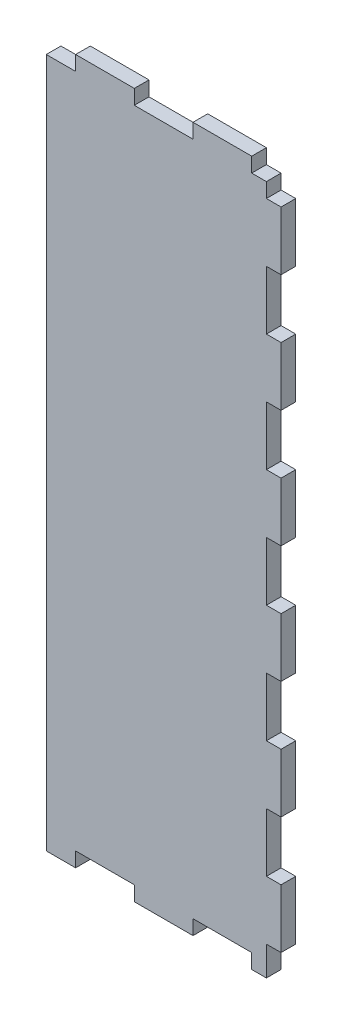
SolidWorks part; units mm, degrees
ref_plane "Front Plane" through (0, 0, 0) normal (0, 0, 1) x (1, 0, 0)
ref_plane "Top Plane" through (0, 0, 0) normal (0, 1, 0) x (1, 0, 0)
ref_plane "Right Plane" through (0, 0, 0) normal (1, 0, 0) x (0, 0, -1)
sketch "Sketch1" plane through (0, 0, 0) normal (0, 0, 1) x (1, 0, 0)
  line L1 (0, 0) -> (50.8, 0)
  line L2 (0, 0) -> (0, 152.4)
  line L3 (0, 152.4) -> (50.8, 152.4)
  line L4 (50.8, 0) -> (50.8, 152.4)
  dimension "D1" = 152.4
  dimension "D2" = 50.8
extrude "Extrude1" add sketch "Sketch1" along normal blind 3.175
sketch "Sketch3" plane through (0, 0, 3.175) normal (0, 0, 1) x (1, 0, 0)
  line L0 (50.8, 0) -> (50.8, 152.4) construction
  line L1 (50.8, 146.05) -> (47.625, 146.05)
  line L2 (50.8, 146.05) -> (50.8, 152.4)
  line L3 (50.8, 152.4) -> (47.625, 152.4)
  line L4 (47.625, 146.05) -> (47.625, 152.4)
  dimension "D1" = 6.35
  dimension "D2" = 3.175
  dimension "D3" = 6.35
extrude "Cut-Extrude1" cut sketch "Sketch3" against normal blind 3.175
pattern_linear "LPattern1" count 2 spacing 146.05 along (0, -1, 0) of "Cut-Extrude1"
sketch "Sketch4" plane through (0, 0, 3.175) normal (0, 0, 1) x (1, 0, 0)
  line L0 (50.8, 6.35) -> (50.8, 146.05) construction
  line L1 (50.8, 133.35) -> (47.625, 133.35)
  line L2 (50.8, 133.35) -> (50.8, 120.65)
  line L3 (50.8, 120.65) -> (47.625, 120.65)
  line L4 (47.625, 133.35) -> (47.625, 120.65)
  line L5 (47.625, 152.4) -> (0, 152.4) construction
  dimension "D1" = 12.7
  dimension "D2" = 3.175
  dimension "D3" = 19.05
extrude "Cut-Extrude2" cut sketch "Sketch4" against normal blind 3.175
pattern_linear "LPattern2" count 5 spacing 25.4 along (0, -1, 0) of "Cut-Extrude2"
sketch "Sketch5" plane through (0, 0, 3.175) normal (0, 0, 1) x (1, 0, 0)
  line L0 (0, 0) -> (47.625, 0) construction
  line L1 (19.05, 0) -> (6.35, 0)
  line L2 (19.05, 0) -> (19.05, 3.175)
  line L3 (19.05, 3.175) -> (6.35, 3.175)
  line L4 (6.35, 0) -> (6.35, 3.175)
  dimension "D1" = 6.35
  dimension "D2" = 12.7
  dimension "D3" = 3.175
extrude "Cut-Extrude3" cut sketch "Sketch5" against normal blind 3.175
sketch "Sketch6" plane through (0, 0, 3.175) normal (0, 0, 1) x (1, 0, 0)
  line L1 (0, 152.4) -> (6.35, 152.4)
  line L2 (0, 152.4) -> (0, 149.225)
  line L3 (0, 149.225) -> (6.35, 149.225)
  line L4 (6.35, 152.4) -> (6.35, 149.225)
  dimension "D1" = 6.35
  dimension "D2" = 3.175
extrude "Cut-Extrude4" cut sketch "Sketch6" against normal blind 3.175
pattern_linear "LPattern3" count 2 spacing 44.45 along (1, 0, 0) of "Cut-Extrude4"
pattern_linear "LPattern4" count 2 spacing 25.4 along (1, 0, 0) of "Cut-Extrude3"
sketch "Sketch7" plane through (0, 0, 3.175) normal (0, 0, 1) x (1, 0, 0)
  line L0 (44.45, 152.4) -> (6.35, 152.4) construction
  line L1 (19.05, 152.4) -> (31.75, 152.4)
  line L2 (19.05, 152.4) -> (19.05, 149.225)
  line L3 (19.05, 149.225) -> (31.75, 149.225)
  line L4 (31.75, 152.4) -> (31.75, 149.225)
  line L5 (0, 149.225) -> (0, 0) construction
  dimension "D1" = 3.175
  dimension "D2" = 12.7
  dimension "D3" = 19.05
extrude "Cut-Extrude5" cut sketch "Sketch7" against normal through all
